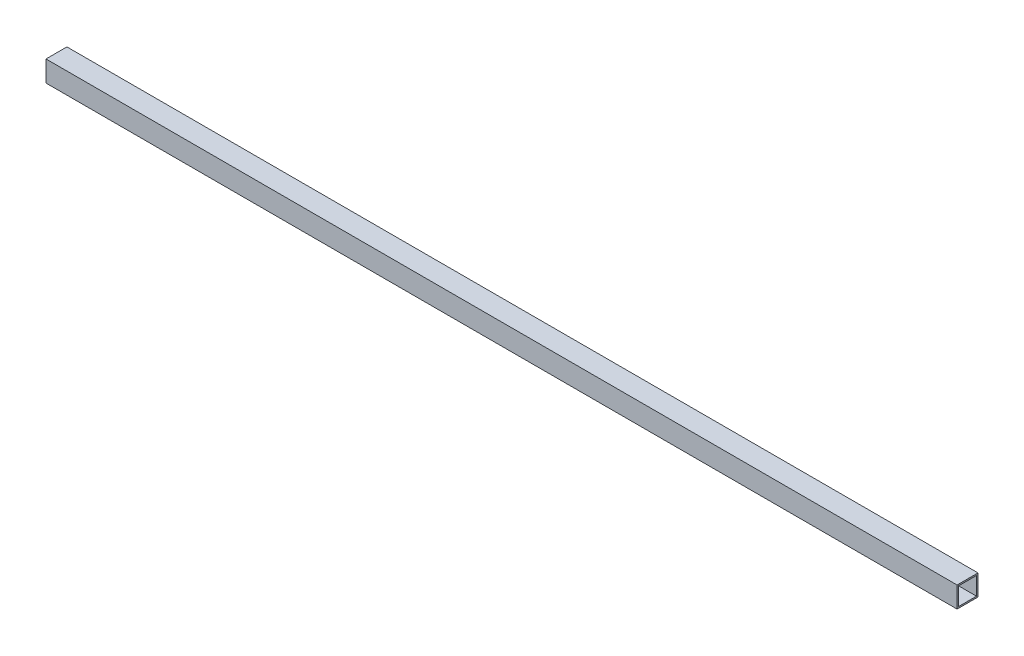
SolidWorks part; units mm, degrees
material "6061 Alloy"
ref_plane "Front Plane" through (0, 0, 0) normal (0, 0, 1) x (1, 0, 0)
ref_plane "Top Plane" through (0, 0, 0) normal (0, 1, 0) x (1, 0, 0)
ref_plane "Right Plane" through (0, 0, 0) normal (1, 0, 0) x (0, 0, -1)
sketch "Sketch1" plane through (0, 0, 0) normal (1, 0, 0) x (0, 0, -1)
  line L1 (0, 0) -> (44.45, 0)
  line L2 (0, 0) -> (0, 44.45)
  line L3 (0, 44.45) -> (44.45, 44.45)
  line L4 (44.45, 0) -> (44.45, 44.45)
  line L5 (3.175, 41.275) -> (41.275, 41.275)
  line L6 (3.175, 41.275) -> (3.175, 3.175)
  line L7 (3.175, 3.175) -> (41.275, 3.175)
  line L8 (41.275, 41.275) -> (41.275, 3.175)
  dimension "D1" = 44.45
  dimension "D2" = 38.1
  dimension "D3" = 3.175
  dimension "D4" = 44.45
  dimension "D5" = 38.1
  dimension "D6" = 3.175
extrude "Boss-Extrude1" add sketch "Sketch1" along normal blind 1936.75
